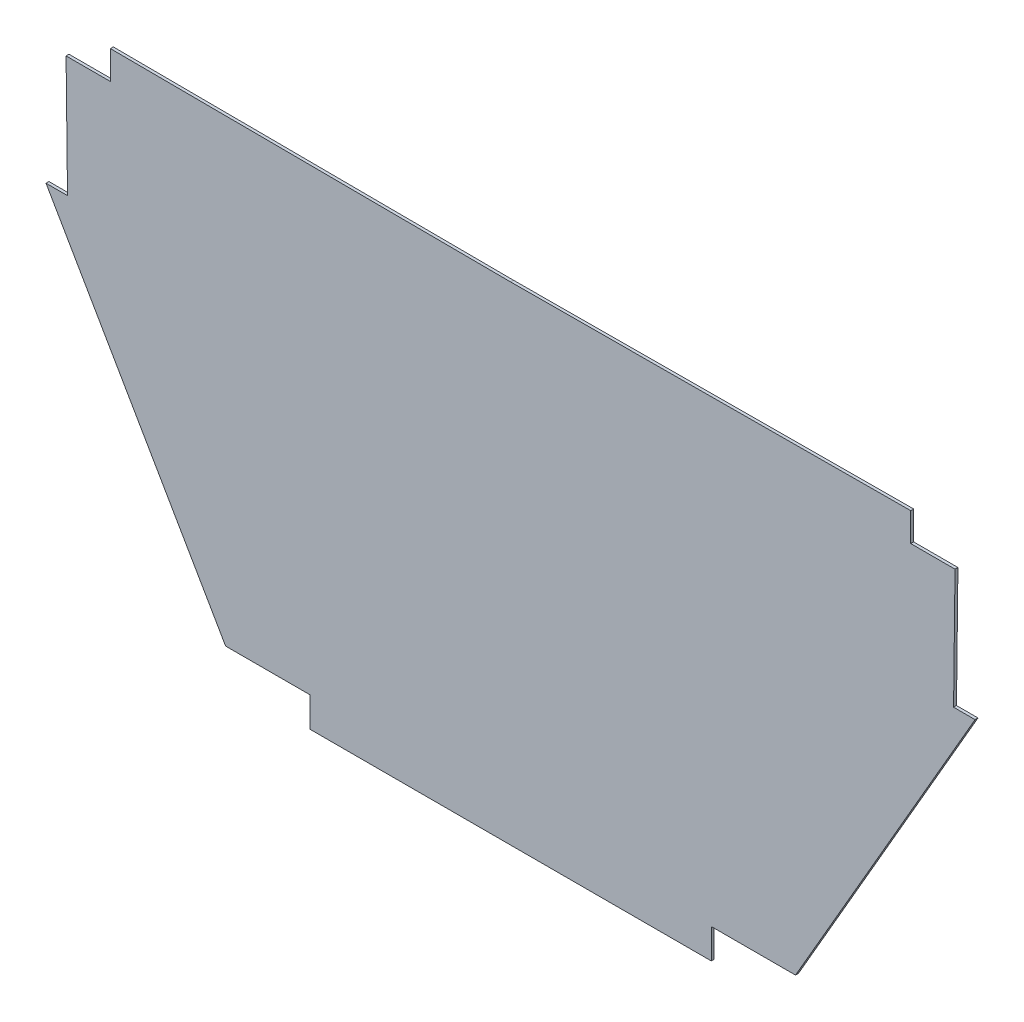
SolidWorks part; units mm, degrees
ref_plane "Front Plane" through (0, 0, 0) normal (0, 0, 1) x (1, 0, 0)
ref_plane "Top Plane" through (0, 0, 0) normal (0, 1, 0) x (1, 0, 0)
ref_plane "Right Plane" through (0, 0, 0) normal (1, 0, 0) x (0, 0, -1)
sketch "Sketch1" plane through (0, 0, 0) normal (0, 0, 1) x (1, 0, 0)
  line L0 (200.633, 424.0953) -> (185.8311, 424.0953)
  line L2 (185.8311, 424.0953) -> (309.3774, 210.107)
  line L3 (309.3774, 210.107) -> (367.2941, 210.107)
  line L4 (367.2941, 210.107) -> (367.2941, 189.577)
  line L5 (367.2941, 189.577) -> (643.5157, 189.577)
  line L6 (505.4049, 525.0868) -> (505.4049, 189.577) construction
  line L7 (505.4049, 189.577) -> (505.4049, 525.0868) construction
  line L8 (230.1165, 526.4554) -> (505.4049, 525.0868)
  line L10 (199.6417, 506.847) -> (200.633, 424.0953)
  line L11 (230.1165, 506.847) -> (199.6417, 506.847)
  line L12 (643.5157, 210.107) -> (643.5157, 189.577)
  line L13 (701.4324, 210.107) -> (643.5157, 210.107)
  line L14 (824.9786, 424.0953) -> (701.4324, 210.107)
  line L15 (810.1767, 424.0953) -> (824.9786, 424.0953)
  line L16 (780.6933, 526.4554) -> (505.4049, 525.0868)
  line L17 (230.1165, 526.4554) -> (230.1165, 506.847)
  line L19 (780.6933, 526.4554) -> (780.6933, 506.847)
  line L20 (780.6933, 506.847) -> (811.1681, 506.847)
  line L21 (811.1681, 506.847) -> (810.1767, 424.0953)
extrude "Boss-Extrude1" add sketch "Sketch1" along normal blind 2 contours L16 L8 L17 L11 L10 L0 L2 L3 L4 L5 L12 L13 L14 L15 L21 L20 L19
